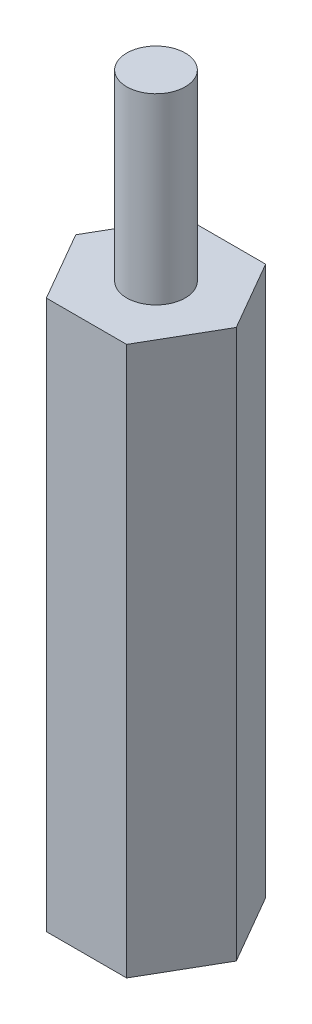
SolidWorks part; units mm, degrees
ref_plane "Front Plane" through (0, 0, 0) normal (0, 0, 1) x (1, 0, 0)
ref_plane "Top Plane" through (0, 0, 0) normal (0, 1, 0) x (1, 0, 0)
ref_plane "Right Plane" through (0, 0, 0) normal (1, 0, 0) x (0, 0, -1)
sketch "Sketch1" plane through (0, 0, 0) normal (0, 1, 0) x (1, 0, 0)
  line L1 (1.3931, -2.413) -> (2.7863, 0)
  line L2 (2.7863, 0) -> (1.3931, 2.413)
  line L3 (1.3931, 2.413) -> (-1.3931, 2.413)
  line L4 (-1.3931, 2.413) -> (-2.7863, 0)
  line L5 (-2.7863, 0) -> (-1.3931, -2.413)
  line L6 (-1.3931, -2.413) -> (1.3931, -2.413)
  circle A0 centre (0, 0) radius 2.413 construction
  dimension "D1" = 4.826
  dimension "D2" = 0
extrude "Boss-Extrude1" add sketch "Sketch1" along normal blind 19.05
sketch "Sketch2" plane through (0, 19.05, 0) normal (0, 1, 0) x (1, 0, 0)
  circle A0 centre (0, 0) radius 1.016
  dimension "D1" = 2.032
extrude "Boss-Extrude2" add sketch "Sketch2" along normal blind 6.35
sketch "Sketch3" plane through (0, 0, 0) normal (0, -1, 0) x (1, 0, 0)
  circle A0 centre (0, 0) radius 1.016
  dimension "D1" = 2.032
extrude "Cut-Extrude1" cut sketch "Sketch3" against normal blind 6.35
